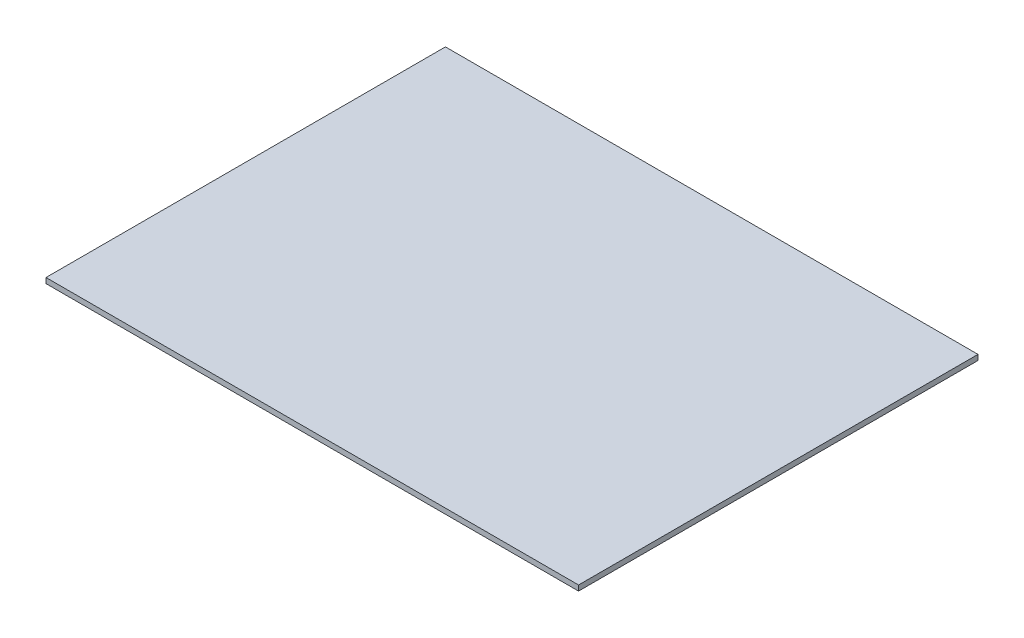
SolidWorks part; units mm, degrees
ref_plane "Спереди" through (0, 0, 0) normal (0, 0, 1) x (1, 0, 0)
ref_plane "Сверху" through (0, 0, 0) normal (0, 1, 0) x (1, 0, 0)
ref_plane "Справа" through (0, 0, 0) normal (1, 0, 0) x (0, 0, -1)
sketch "Эскиз1" plane through (0, 0, 0) normal (0, 1, 0) x (1, 0, 0)
  line L1 (-200, -150) -> (200, -150)
  line L2 (-200, -150) -> (-200, 150)
  line L3 (-200, 150) -> (200, 150)
  line L4 (200, -150) -> (200, 150)
  line L5 (-200, -150) -> (200, 150) construction
  line L6 (-200, 150) -> (200, -150) construction
  point P0 (0, 0)
  dimension "D1" = 300
  dimension "D2" = 400
extrude "Бобышка-Вытянуть1" add sketch "Эскиз1" along normal blind 4
